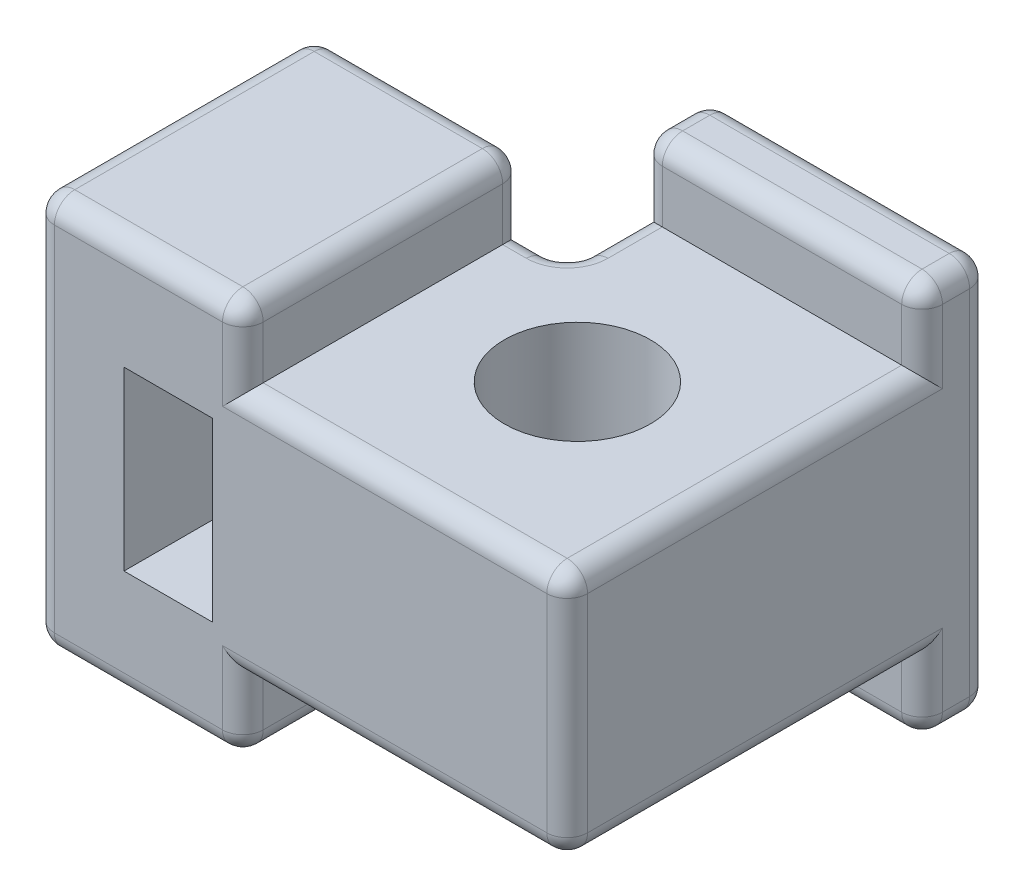
SolidWorks part; units mm, degrees
ref_plane "Front" through (0, 0, 0) normal (0, 0, 1) x (1, 0, 0)
ref_plane "Top" through (0, 0, 0) normal (0, 1, 0) x (1, 0, 0)
ref_plane "Right" through (0, 0, 0) normal (1, 0, 0) x (0, 0, -1)
sketch "Sketch1" plane through (0, 0, 0) normal (0, 1, 0) x (1, 0, 0)
  line L0 (-11.1125, 3.81) -> (-4.191, 3.81)
  line L1 (-4.191, 3.81) -> (-4.191, 9.144)
  line L2 (-4.191, 9.144) -> (6.2865, 9.144)
  line L3 (6.2865, 9.144) -> (6.2865, -6.6675)
  line L4 (6.2865, -6.6675) -> (-11.1125, -6.6675)
  line L5 (-11.1125, -6.6675) -> (-11.1125, 3.81)
  line L7 (0, 9.144) -> (0, 0) construction
  line L8 (-11.1125, 0) -> (0, 0) construction
  circle A0 centre (0, 0) radius 2.7305
  dimension "D1" = 5.461
  dimension "D2" = 10.4775
  dimension "D3" = 11.1125
  dimension "D4" = 9.144
  dimension "D5" = 5.334
  dimension "D6" = 17.399
extrude "Boss-Extrude1" add sketch "Sketch1" along normal mid plane 9.271
sketch "Sketch2" plane through (-11.1125, 0, 0) normal (-1, 0, 0) x (0, 0, 1)
  line L1 (-3.81, 4.6355) -> (6.6675, 4.6355)
  line L2 (-3.81, 4.6355) -> (-3.81, -4.6355)
  line L3 (-3.81, -4.6355) -> (6.6675, -4.6355)
  line L4 (6.6675, 4.6355) -> (6.6675, -4.6355)
extrude "Boss-Extrude2" add sketch "Sketch2" along normal blind 2.54
sketch "Sketch3" plane through (0, 0, 0) normal (0, 1, 0) x (1, 0, 0)
  line L0 (6.2865, 9.144) -> (6.2865, -6.6675) construction
  line L1 (6.2865, 6.604) -> (-4.191, 6.604)
  line L2 (6.2865, 6.604) -> (6.2865, 9.144)
  line L3 (6.2865, 9.144) -> (-4.191, 9.144)
  line L4 (-4.191, 6.604) -> (-4.191, 9.144)
  line L5 (-4.191, 9.144) -> (6.2865, 9.144) construction
  line L6 (-4.191, 3.81) -> (-4.191, 9.144) construction
  line L8 (-5.842, -6.6675) -> (-13.6525, -6.6675)
  line L9 (-5.842, -6.6675) -> (-5.842, 3.81)
  line L10 (-5.842, 3.81) -> (-13.6525, 3.81)
  line L11 (-13.6525, -6.6675) -> (-13.6525, 3.81)
  line L12 (-13.6525, -6.6675) -> (-13.6525, 3.81) construction
  line L13 (6.2865, -6.6675) -> (-11.1125, -6.6675) construction
  line L14 (-11.1125, 3.81) -> (-4.191, 3.81) construction
  line L15 (0, 9.144) -> (0, 0) construction
  circle A0 centre (0, 0) radius 2.7305 construction
  dimension "D1" = 6.604
  dimension "D2" = 5.842
extrude "Boss-Extrude3" add sketch "Sketch3" along normal mid plane 14.732
sketch "Sketch4" plane through (0, 0, -3.81) normal (0, 0, -1) x (-1, 0, 0)
  line L0 (3.6195, 0) -> (13.6525, 0) construction
  line L1 (6.985, 3.302) -> (10.287, 3.302)
  line L2 (6.985, 3.302) -> (6.985, -3.302)
  line L3 (6.985, -3.302) -> (10.287, -3.302)
  line L4 (10.287, 3.302) -> (10.287, -3.302)
  line L5 (13.6525, 7.366) -> (13.6525, -7.366) construction
  line L6 (4.191, 4.6355) -> (4.191, -4.6355) construction
  line L7 (8.636, 3.302) -> (8.636, -3.302) construction
  point P12 (8.636, 0)
  dimension "D1" = 3.302
  dimension "D2" = 6.604
  dimension "D3" = 4.445
extrude "Cut-Extrude1" cut sketch "Sketch4" against normal up to surface (10.4775 mm away) up to face at (-4.7625, 0, 6.6675)
fillet "Fillet1" radius 0.762 38 edges at (-9.7472, 7.366, 6.6675) (-9.7472, 7.366, -3.81) (6.2865, 7.366, -7.874) (-4.191, 7.366, -7.874) (1.0478, 7.366, -9.144) (-13.6525, 7.366, 1.4287) (-13.6525, 0, 6.6675) (-13.6525, 0, -3.81) (-4.191, 0, -9.144) (6.2865, 0, -9.144) (-9.7472, -7.366, 6.6675) (-13.6525, -7.366, 1.4287) (-9.7472, -7.366, -3.81) (-4.191, -7.366, -7.874) (1.0478, -7.366, -9.144) (6.2865, -7.366, -7.874) (6.2865, 0, 6.6675) (6.2865, -4.6355, 0.0318) (0.2223, -4.6355, 6.6675) (6.2865, 4.6355, 0.0318) (0.2223, 4.6355, 6.6675) (-5.0165, -4.6355, -3.81) (-4.191, -4.6355, -5.207) (-5.0165, 4.6355, -3.81) (-4.191, 4.6355, -5.207) (-5.842, 7.366, 1.4288) (1.0478, 7.366, -6.604) (6.2865, 6.0008, -6.604) (-5.842, 6.0008, 6.6675) (-5.842, -6.0008, 6.6675) (6.2865, -6.0008, -6.604) (-4.191, 6.0008, -6.604) (-5.842, 6.0008, -3.81) (1.0478, -7.366, -6.604) (-4.191, -6.0008, -6.604) (-5.842, -7.366, 1.4288) (-5.842, -6.0008, -3.81) (-4.191, 0, -3.81)
